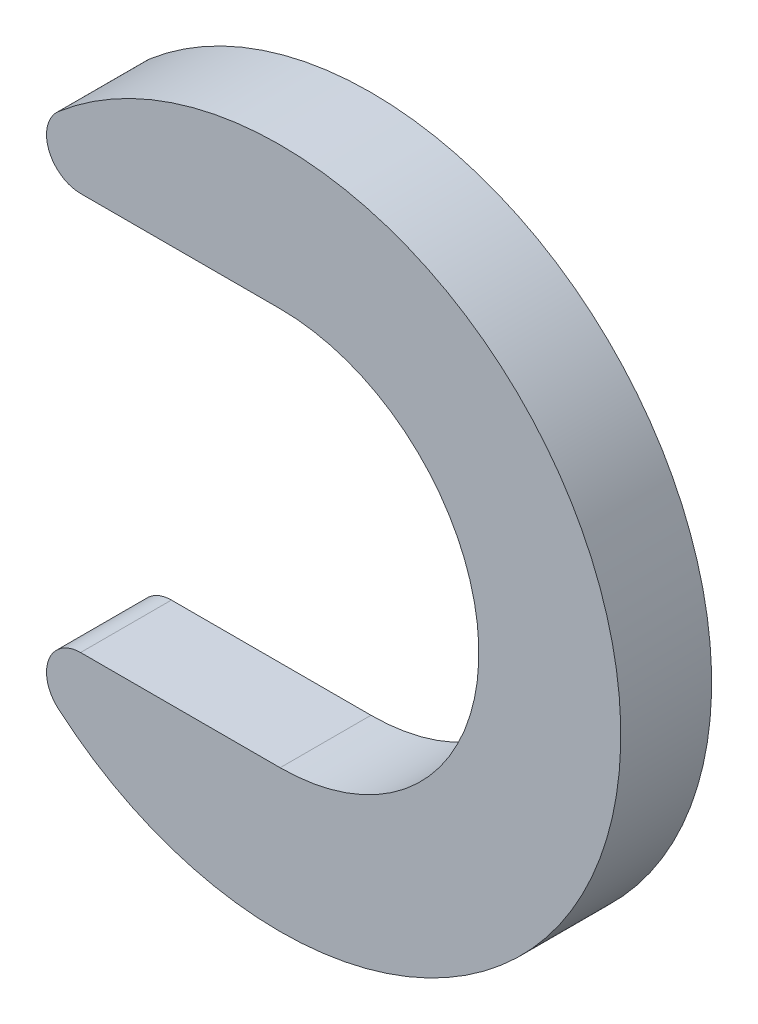
SolidWorks part; units mm, degrees
ref_plane "Plane1" through (0, 0, 0) normal (0, 0, 1) x (1, 0, 0)
ref_plane "Plane2" through (0, 0, 0) normal (0, 1, 0) x (1, 0, 0)
ref_plane "Plane3" through (0, 0, 0) normal (1, 0, 0) x (0, 0, -1)
sketch "Sketch1" plane through (0, 0, 0) normal (0, 0, 1) x (1, 0, 0)
  line L0 (-17.5713, -17.5) -> (0, -17.5)
  line L4 (0, 0) -> (32, 0) construction
  line L8 (-17.5713, 17.5) -> (0, 17.5)
  arc A0 (0, 17.5) -> (0, -17.5) centre (0, 0) cw
  arc A1 (-17.5713, 17.5) -> (-19.5236, 22.7778) centre (-17.5713, 20.5) cw
  arc A2 (-17.5713, -17.5) -> (-19.5236, -22.7778) centre (-17.5713, -20.5) ccw
  arc A5 (-19.5236, -22.7778) -> (-19.5236, 22.7778) centre (0, 0) ccw
  point P9 (-24.367, 17.5)
  point P12 (-24.367, -17.5)
  dimension "D1" = 30
  dimension "D4" = 17.5
  dimension "D2" = 3
extrude "Base-Extrude" add sketch "Sketch1" along normal blind 8
